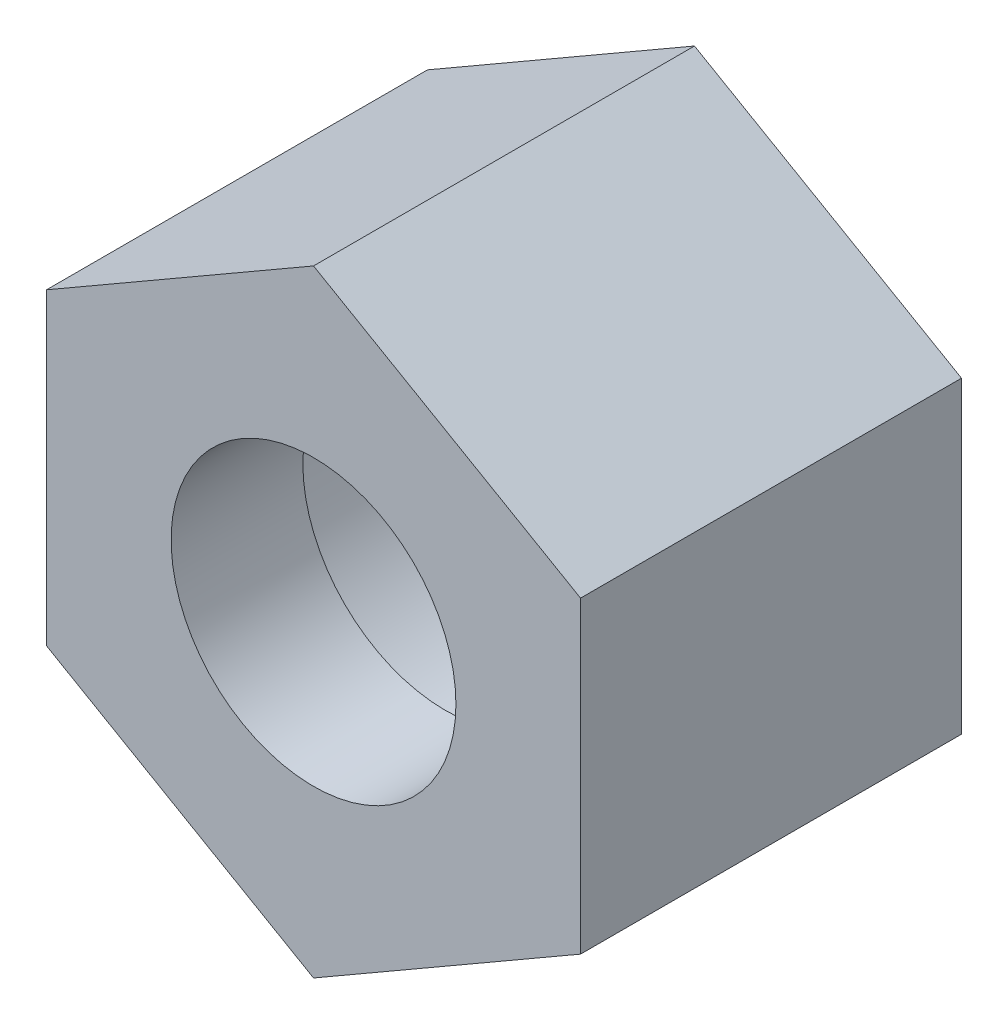
SolidWorks part; units mm, degrees
ref_plane "Plane1" through (0, 0, 0) normal (0, 0, 1) x (1, 0, 0)
ref_plane "Plane2" through (0, 0, 0) normal (0, 1, 0) x (1, 0, 0)
ref_plane "Plane3" through (0, 0, 0) normal (1, 0, 0) x (0, 0, -1)
sketch "Sketch1" plane through (0, 0, 0) normal (0, 0, 1) x (1, 0, 0)
  line L1 (0, 17.3205) -> (-15, 8.6603)
  line L2 (-15, 8.6603) -> (-15, -8.6603)
  line L3 (-15, -8.6603) -> (0, -17.3205)
  line L4 (0, -17.3205) -> (15, -8.6603)
  line L5 (15, -8.6603) -> (15, 8.6603)
  line L6 (15, 8.6603) -> (0, 17.3205)
  circle A0 centre (0, 0) radius 15 construction
  dimension "Nøglevidde" = 30
extrude "Base-Extrude" add sketch "Sketch1" along normal blind 21.4
sketch "Sketch2" plane through (0, 0, 0) normal (0, 0, -1) x (-1, 0, 0)
  circle A0 centre (0, 0) radius 11.25
  dimension "Gev.dia." = 22.5
extrude "Cut-Extrude1" cut sketch "Sketch2" against normal blind 14
sketch "Sketch3" plane through (0, 0, 21.4) normal (0, 0, 1) x (1, 0, 0)
  circle A0 centre (0, 0) radius 8
  dimension "Diameter" = 16
extrude "Cut-Extrude2" cut sketch "Sketch3" against normal through all
